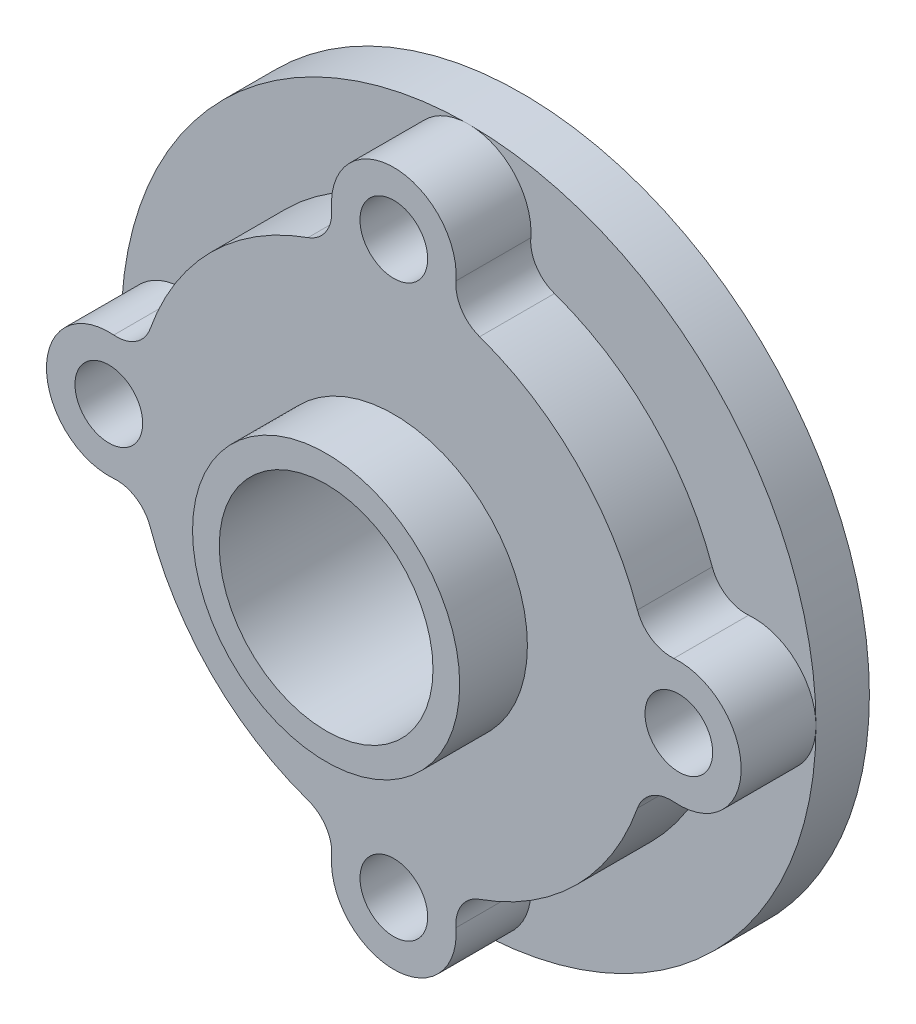
SolidWorks part; units mm, degrees
ref_plane "前视基准面" through (0, 0, 0) normal (0, 0, 1) x (1, 0, 0)
ref_plane "上视基准面" through (0, 0, 0) normal (0, 1, 0) x (1, 0, 0)
ref_plane "右视基准面" through (0, 0, 0) normal (1, 0, 0) x (0, 0, -1)
sketch "草图1" plane through (0, 0, 0) normal (0, 0, 1) x (1, 0, 0)
  circle A0 centre (0, 0) radius 97.5
  dimension "D1" = 195
extrude "凸台-拉伸1" add sketch "草图1" along normal blind 15
sketch "草图2" plane through (0, 0, 15) normal (0, 0, 1) x (1, 0, 0)
  circle A0 centre (0, 0) radius 72.5
  dimension "D1" = 145
extrude "凸台-拉伸2" add sketch "草图2" along normal blind 21
sketch "草图3" plane through (0, 0, 0) normal (0, 0, -1) x (-1, 0, 0)
  circle A0 centre (0, 0) radius 67.5
  dimension "D1" = 135
extrude "凸台-拉伸3" add sketch "草图3" along normal blind 12
sketch "草图4" plane through (0, 0, 36) normal (0, 0, 1) x (1, 0, 0)
  circle A0 centre (0, 0) radius 37.5
  dimension "D1" = 75
extrude "凸台-拉伸4" add sketch "草图4" along normal blind 19 contours A0
sketch "草图5" plane through (0, 0, 55) normal (0, 0, 1) x (1, 0, 0)
  circle A0 centre (0, 0) radius 30
  dimension "D1" = 60
extrude "切除-拉伸1" cut sketch "草图5" against normal up to next
sketch "草图6" plane through (0, 0, -12) normal (0, 0, -1) x (-1, 0, 0)
  circle A2 centre (0, 0) radius 57.5
  circle A3 centre (0, 0) radius 57.5
  dimension "D1" = 10
extrude "切除-拉伸2" cut sketch "草图6" against normal blind 5
sketch "草图7" plane through (0, 0, -7) normal (0, 0, -1) x (-1, 0, 0)
  circle A0 centre (0, 0) radius 57.5 construction
  circle A1 centre (0, 0) radius 57.5
  circle A5 centre (0, 0) radius 37.5
  circle A6 centre (0, 0) radius 37.5
  dimension "D1" = 7.5
extrude "切除-拉伸3" cut sketch "草图7" against normal blind 20
sketch "草图8" plane through (0, 0, 15) normal (0, 0, 1) x (1, 0, 0)
  line L0 (0, 97.5) -> (0, -97.5) construction
  line L1 (-97.5, 0) -> (97.5, 0) construction
  circle A0 centre (0, 0) radius 97.5 construction
  circle A1 centre (0, 0) radius 80 construction
  arc A2 (17.4445, 78.608) -> (-17.4445, 78.608) centre (0, 80) ccw
  arc A3 (78.608, -17.4445) -> (78.608, 17.4445) centre (80, 0) ccw
  arc A4 (-17.4445, -78.608) -> (17.4445, -78.608) centre (0, -80) ccw
  arc A5 (-78.608, 17.4445) -> (-78.608, -17.4445) centre (-80, 0) ccw
  arc A6 (24.0901, 68.3807) -> (-24.0901, 68.3807) centre (0, 0) ccw
  arc A12 (-24.0901, -68.3807) -> (24.0901, -68.3807) centre (0, 0) ccw
  arc A17 (-24.0901, -68.3807) -> (-17.4445, -78.608) centre (-27.4129, -77.8125) cw
  arc A18 (17.4445, -78.608) -> (24.0901, -68.3807) centre (27.4129, -77.8125) cw
  arc A19 (68.3807, -24.0901) -> (78.608, -17.4445) centre (77.8125, -27.4129) cw
  arc A20 (78.608, 17.4445) -> (68.3807, 24.0901) centre (77.8125, 27.4129) cw
  arc A21 (24.0901, 68.3807) -> (17.4445, 78.608) centre (27.4129, 77.8125) cw
  arc A22 (-24.0901, 68.3807) -> (-17.4445, 78.608) centre (-27.4129, 77.8125) ccw
  arc A23 (-68.3807, 24.0901) -> (-78.608, 17.4445) centre (-77.8125, 27.4129) cw
  arc A24 (-68.3807, -24.0901) -> (-78.608, -17.4445) centre (-77.8125, -27.4129) ccw
  circle A25 centre (0, 0) radius 72.5 construction
  arc A26 (-68.3807, 24.0901) -> (-68.3807, -24.0901) centre (0, 0) ccw
  arc A27 (68.3807, -24.0901) -> (68.3807, 24.0901) centre (0, 0) ccw
  dimension "D1" = 160
  dimension "D2" = 10
extrude "凸台-拉伸5" add sketch "草图8" along normal up to surface (21 mm away) up to face at (37.5, 0, 36)
sketch "草图9" plane through (0, 0, 36) normal (0, 0, 1) x (1, 0, 0)
  line L0 (0, 97.5) -> (0, -97.5) construction
  line L1 (-97.5, 0) -> (97.5, 0) construction
  circle A0 centre (0, 0) radius 80 construction
  arc A1 (78.608, -17.4445) -> (78.608, 17.4445) centre (80, 0) ccw construction
  circle A2 centre (0, 80) radius 9.5
  circle A3 centre (80, 0) radius 9.5
  circle A4 centre (0, -80) radius 9.5
  circle A5 centre (-80, 0) radius 9.5
  dimension "D1" = 160
  dimension "D2" = 19
  dimension "D3" = 19
  dimension "D4" = 19
  dimension "D5" = 19
extrude "切除-拉伸4" cut sketch "草图9" against normal up to surface (36 mm away) up to face at (-67.5, 0, 0)
